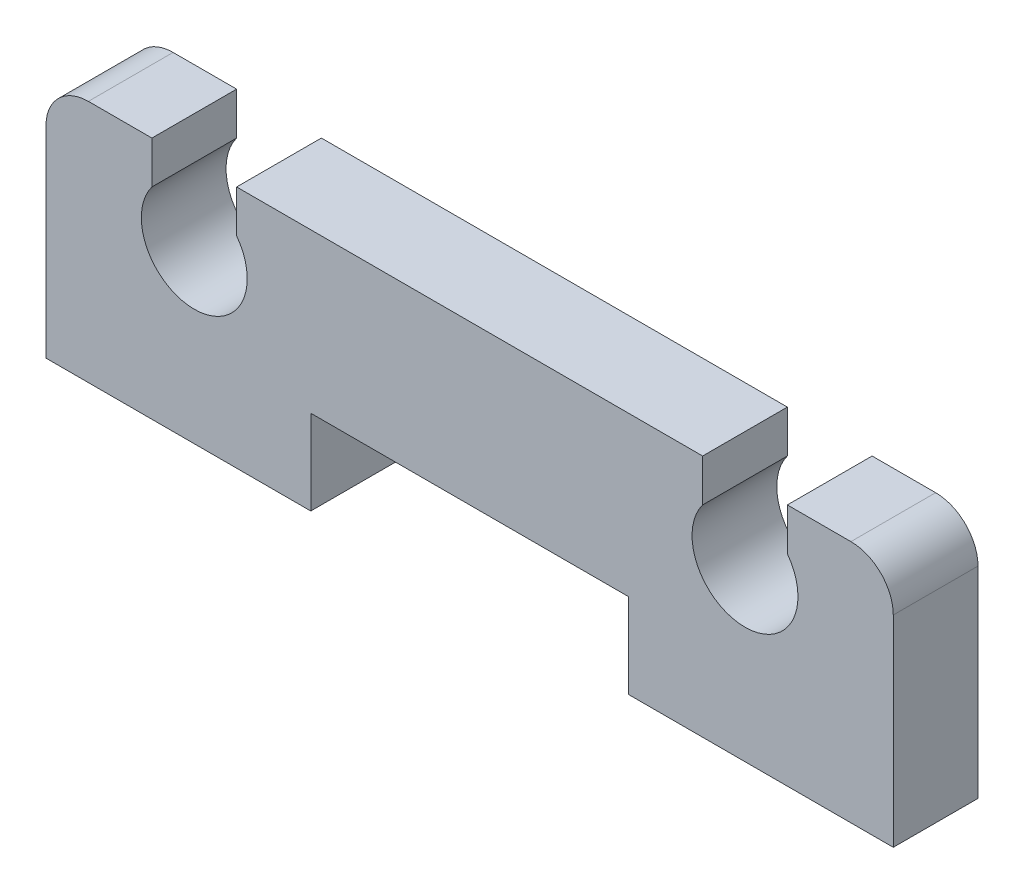
SolidWorks part; units mm, degrees
ref_plane "Front Plane" through (0, 0, 0) normal (0, 0, 1) x (1, 0, 0)
ref_plane "Top Plane" through (0, 0, 0) normal (0, 1, 0) x (1, 0, 0)
ref_plane "Right Plane" through (0, 0, 0) normal (1, 0, 0) x (0, 0, -1)
sketch "Sketch1" plane through (0, 0, 0) normal (0, 0, 1) x (1, 0, 0)
  line L14 (-10, 0) -> (-10, 5.75)
  line L15 (-10, 5.75) -> (-7.5, 5.75)
  line L16 (-10, 0) -> (-3.75, 0)
  line L17 (-3.75, 0) -> (-3.75, 2)
  line L18 (-3.75, 2) -> (3.75, 2)
  line L19 (0, 5.75) -> (0, 0) construction
  line L20 (-7.5, 4.75) -> (-7.5, 5.75)
  line L21 (-5.5, 4.75) -> (-5.5, 5.75)
  line L22 (-5.5, 5.75) -> (5.5, 5.75)
  line L23 (5.5, 4.75) -> (5.5, 5.75)
  line L24 (7.5, 4.75) -> (7.5, 5.75)
  line L25 (3.75, 0) -> (3.75, 2)
  line L26 (10, 0) -> (3.75, 0)
  line L27 (10, 5.75) -> (7.5, 5.75)
  line L28 (10, 0) -> (10, 5.75)
  arc A4 (-7.5, 4.75) -> (-5.5, 4.75) centre (-6.5, 4) ccw
  arc A5 (7.5, 4.75) -> (5.5, 4.75) centre (6.5, 4) cw
  point P41 (0, 2)
  dimension "D2" = 10
  dimension "D10" = 1.25
  dimension "D3" = 2
  dimension "D4" = 1.75
  dimension "D5" = 2
  dimension "D6" = 5.75
  dimension "D7" = 6.25
  dimension "D9" = 3.5
extrude "Tube Plate Body" add sketch "Sketch1" along normal blind 2
fillet "Tube Plate Contouring" radius 1 2 edges at (10, 5.75, 1) (-10, 5.75, 1)
equation "\"D2@Sketch1\"=\"Wph@Parameters@RobotHandParameters.SLDPRT\"/2"
equation "\"D6@Sketch1\"=\"rp@Parameters@RobotHandParameters.SLDPRT\" - 2 - \"Tjointp@Parameters@RobotHandParameters.SLDPRT\"/2 + 1.75"
